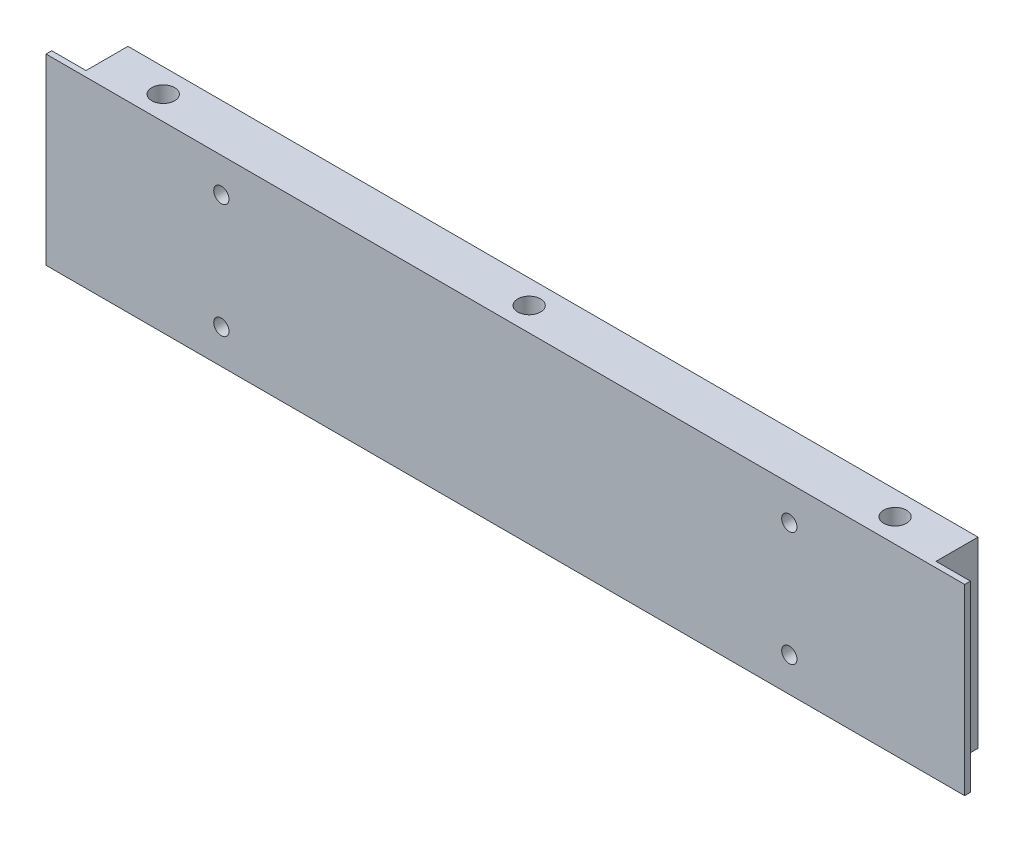
SolidWorks part; units mm, degrees
ref_plane "Plan de face" through (0, 0, 0) normal (0, 0, 1) x (1, 0, 0)
ref_plane "Plan de dessus" through (0, 0, 0) normal (0, 1, 0) x (1, 0, 0)
ref_plane "Plan de droite" through (0, 0, 0) normal (1, 0, 0) x (0, 0, -1)
sketch "Esquisse1" plane through (0, 0, 0) normal (0, 0, 1) x (1, 0, 0)
  line L0 (0, 0) -> (241, 0)
  line L1 (0, 0) -> (0, -48)
  line L2 (0, -48) -> (241, -48)
  line L3 (241, 0) -> (241, -48)
  line L4 (10.5, 0) -> (10.5, -48) construction
  line L7 (0, -24) -> (241, -24) construction
  circle A5 centre (195, -39) radius 2
  circle A6 centre (46, -9) radius 2
  circle A8 centre (46, -39) radius 2
  circle A9 centre (195, -9) radius 2
  dimension "D1" = 48
  dimension "D6" = 4
  dimension "D7" = 4
  dimension "D9" = 9
  dimension "D10" = 46
  dimension "D11" = 46
  dimension "D12" = 9
  dimension "D22" = 46
  dimension "D23" = 46
  dimension "D24" = 4
  dimension "D25" = 4
  dimension "D2" = 10.5
  dimension "D13" = 241
  dimension "D20" = 9
  dimension "D21" = 9
extrude "Extrusion1" add sketch "Esquisse1" along normal blind 12.5
sketch "Esquisse2" plane through (0, 0, 0) normal (0, 1, 0) x (1, 0, 0)
  line L0 (120.5, -12.5) -> (120.5, 0) construction
  line L1 (241, 0) -> (0, 0) construction
  line L2 (241, -12.5) -> (0, -12.5) construction
  line L3 (9, -11) -> (0, -11)
  line L4 (0, -12.5) -> (0, 0) construction
  line L5 (0, -11) -> (0, 0)
  line L6 (0, 0) -> (9, 0)
  line L7 (241, 0) -> (0, 0) construction
  line L8 (9, 0) -> (9, -11)
  line L9 (232, 0) -> (232, -11)
  line L10 (241, 0) -> (232, 0)
  line L11 (241, -11) -> (241, 0)
  line L12 (232, -11) -> (241, -11)
  dimension "D1" = 9
  dimension "D2" = 11
extrude "Extrusion2" cut sketch "Esquisse2" against normal through all
sketch "Esquisse3" plane through (0, 0, 0) normal (0, 1, 0) x (1, 0, 0)
  line L0 (9, -6.25) -> (232, -6.25) construction
  line L1 (9, -11) -> (9, 0) construction
  line L2 (232, 0) -> (232, -11) construction
  line L3 (120.5, 0) -> (120.5, -12.5) construction
  line L4 (232, 0) -> (9, 0) construction
  line L5 (241, -12.5) -> (0, -12.5) construction
  circle A0 centre (120.5, -6.25) radius 3
  circle A1 centre (24.5, -6.25) radius 3
  circle A2 centre (216.5, -6.25) radius 3
  dimension "D2" = 6
  dimension "D1" = 6.25
  dimension "D3" = 15.5
extrude "Extrusion3" cut sketch "Esquisse3" against normal up to next
